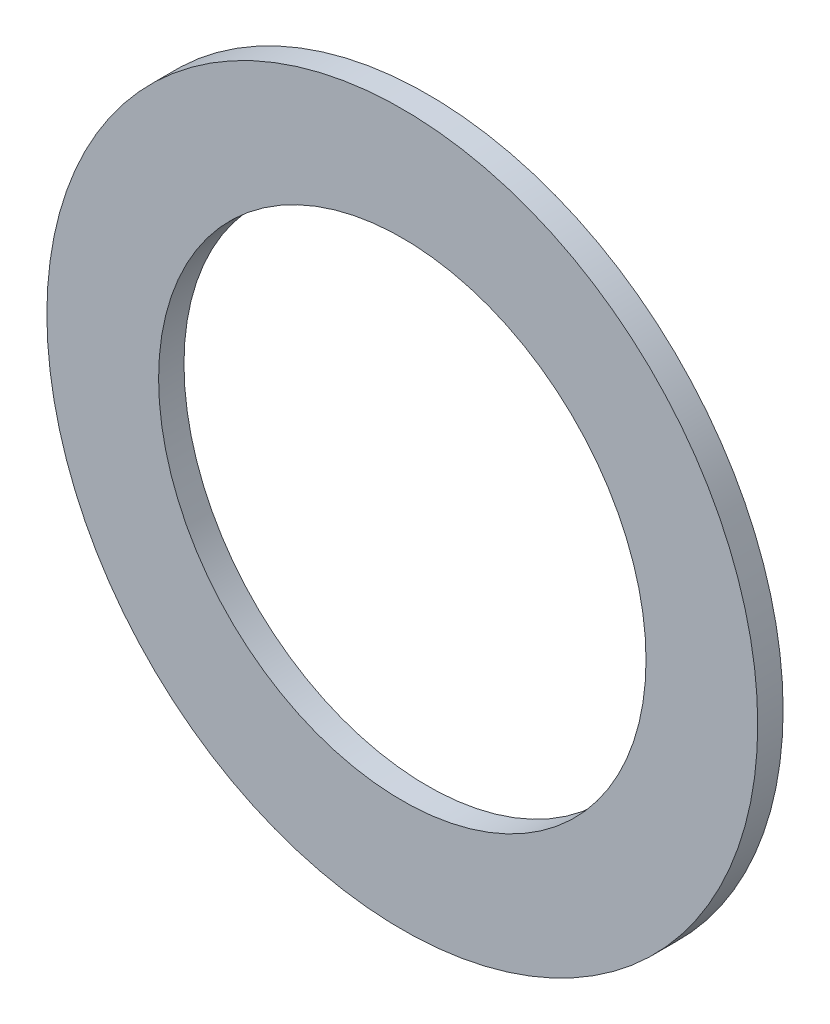
SolidWorks part; units mm, degrees
ref_plane "Plan de face" through (0, 0, 0) normal (0, 0, 1) x (1, 0, 0)
ref_plane "Plan de dessus" through (0, 0, 0) normal (0, 1, 0) x (1, 0, 0)
ref_plane "Plan de droite" through (0, 0, 0) normal (1, 0, 0) x (0, 0, -1)
sketch "Esquisse1" plane through (0, 0, 0) normal (0, 0, 1) x (1, 0, 0)
  circle A0 centre (-0.8518, 0) radius 24
  circle A1 centre (-0.8518, 0) radius 35
extrude "Boss.-Extru.1" add sketch "Esquisse1" along normal blind 2.5
